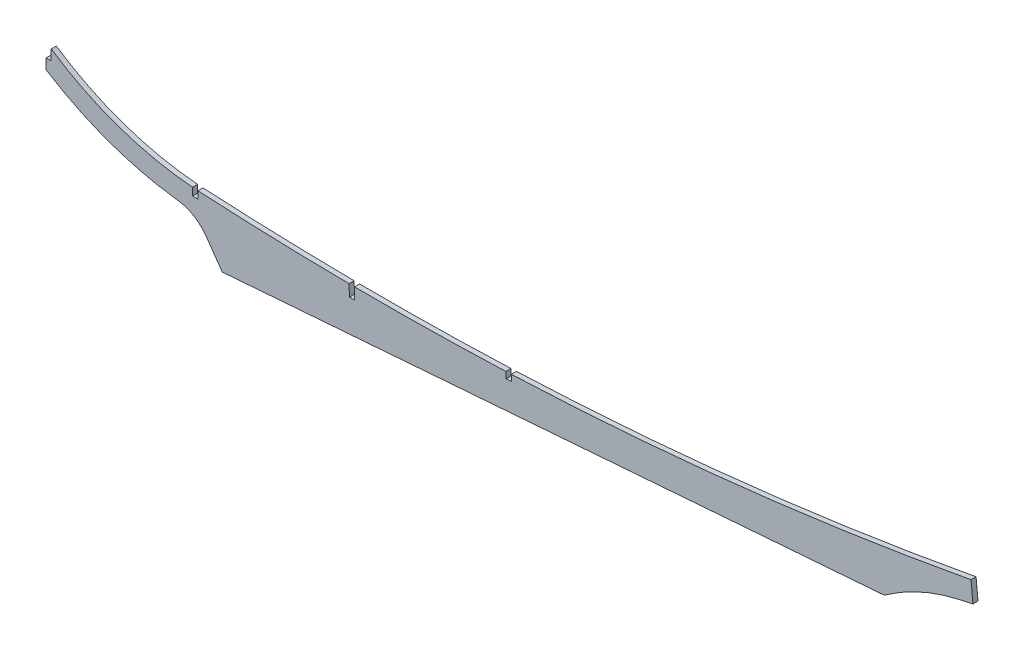
SolidWorks part; units mm, degrees
material "Plywood"
ref_plane "Front Plane" through (0, 0, 0) normal (0, 0, 1) x (1, 0, 0)
ref_plane "Top Plane" through (0, 0, 0) normal (0, 1, 0) x (1, 0, 0)
ref_plane "Right Plane" through (0, 0, 0) normal (1, 0, 0) x (0, 0, -1)
sketch "Sketch1" plane through (0, 0, 0) normal (0, 0, 1) x (1, 0, 0)
  line L0 (0, 0) -> (0, -82.26) construction
  line L1 (0, -194.8549) -> (0, 194.8549) construction
  line L2 (0, -97.5) -> (0, -91.4585)
  line L3 (93.98, 0) -> (93.98, -189.8775) construction
  line L4 (93.98, -128.27) -> (110.9865, -152.3377)
  line L5 (110.9865, -152.3377) -> (126.0572, -151.1732)
  line L6 (176.9893, -147.2378) -> (184.6207, -146.6482)
  line L7 (187.8005, -146.4025) -> (241.2203, -142.2748)
  line L8 (354.9586, -133.4865) -> (362.6867, -132.8893)
  line L9 (365.8665, -132.6436) -> (377.9741, -131.7081)
  line L10 (384.3024, -131.2191) -> (404.1694, -129.684)
  line L11 (408.5302, -129.3471) -> (419.9272, -128.4665)
  line L12 (441.1767, -126.8246) -> (527.7101, -120.1383)
  line L13 (441.1767, -126.8246) -> (527.7101, -120.1383)
  line L14 (110.9865, -152.3377) -> (527.7101, -120.1383)
  line L17 (527.7101, -120.1383) -> (550.2893, -104.3281)
  line L18 (583.5231, -97.0014) -> (582.2981, -84.3606)
  line L20 (110.9865, -152.3377) -> (126.0572, -151.1732)
  line L21 (550.2893, -104.3281) -> (583.5231, -97.0014)
  line L22 (0, 0) -> (690.5062, 0) construction
  line L23 (0, -91.4585) -> (3.81, -91.4585) construction
  line L24 (3.81, -91.4585) -> (3.81, -80.8129) construction
  line L25 (3.81, -84.8545) -> (0, -84.8545) construction
  line L26 (3.81, -91.4585) -> (3.81, -84.8545) construction
  line L27 (0, -84.8545) -> (0, -91.4585)
  line L28 (0, -91.4585) -> (0, -97.5) construction
  line L29 (0, -91.4585) -> (0, -84.8545) construction
  line L30 (0, -84.8545) -> (0, -82.26)
  line L31 (0, -82.26) -> (0, -84.8545) construction
  line L38 (278.6167, 141.3229) -> (279.2722, 126.0923)
  line L39 (189.035, 125.5168) -> (188.7159, 140.759) construction
  line L44 (185.8587, 125.447) -> (185.5396, 140.6895) construction
  line L57 (-1252.8442, 2935.2214) -> (-1204.869, 2833.9344) construction
  line L58 (281.7973, 141.4651) -> (282.4528, 126.2352)
  line L85 (185.8587, 125.447) -> (185.5396, 140.6895)
  line L88 (281.7973, 141.4651) -> (282.4528, 126.2352)
  line L89 (189.035, 125.5168) -> (188.7159, 140.759)
  line L91 (278.6167, 141.3229) -> (279.2722, 126.0923)
  arc A0 (0, -97.5) -> (93.98, -128.27) centre (107.2351, 71.12) ccw
  arc A1 (94.4926, -128.7218) -> (584.0826, -96.9366) centre (241.9639, 1386.2596) ccw construction
  arc A2 (3.81, -84.8545) -> (93.98, -115.5591) centre (107.2351, 71.12) ccw
  arc A3 (93.98, -115.5591) -> (582.2981, -84.3606) centre (209.0039, 1921.2601) ccw
  arc A4 (0, -82.26) -> (3.81, -84.8545) centre (107.2351, 71.12) ccw
  spline S0 degree 3 poles (188.7159, 140.759) (187.6572, 140.7359) (186.5984, 140.7127) (185.5396, 140.6895) knots 0 0 0 0 1 1 1 1 weights 1 1 1 1 construction
  spline S2 degree 3 poles (189.035, 125.5168) (187.9762, 125.4935) (186.9175, 125.4703) (185.8587, 125.447) knots 0 0 0 0 1 1 1 1 weights 1 1 1 1 construction
  spline S3 degree 3 poles (-1210.9259, -106.63) (-2775.9692, 118.2909) (2329.5489, 658.1971) (1983.6341, 70.2608) knots -1490.121028 -1490.121028 -1490.121028 -1490.121028 1121.542395 1121.542395 1121.542395 1121.542395 weights 3.048098 0.655832 0.359268 2.158404 only from (279.2722, 126.0923) to (282.4528, 126.2352)
  spline S5 degree 3 poles (2168.2812, 62.4493) (4677.1606, 1372.865) (-4077.6559, 154.0571) (-1330.4861, -129.027) knots -1401.84833 -1401.84833 -1401.84833 -1401.84833 1857.548452 1857.548452 1857.548452 1857.548452 weights 2.435358 0.211279 0.571848 3.517068 only from (281.7973, 141.4651) to (278.6167, 141.3229)
  spline S6 degree 3 poles (281.7973, 141.4651) (280.7371, 141.4178) (279.6769, 141.3704) (278.6167, 141.3229) knots 0 0 0 0 1 1 1 1 weights 1 1 1 1
  spline S7 degree 3 poles (279.2722, 126.0923) (280.3324, 126.14) (281.3926, 126.1876) (282.4528, 126.2352) knots 0 0 0 0 1 1 1 1 weights 1 1 1 1
  spline S9 degree 3 poles (3542.3692, 39.0953) (16953.6126, 2011.7323) (-10837.86, 256.2836) (-2684.9696, -115.914) knots -2918.044239 -2918.044239 -2918.044239 -2918.044239 3468.374997 3468.374997 3468.374997 3468.374997 weights 2.87602 0.139254 0.396818 3.648687 only from (189.035, 125.5168) to (185.8587, 125.447)
  spline S11 degree 3 poles (3867.0854, 32.7872) (100614.6923, 11738.557) (-16777.5539, 397.4867) (-2961.2542, -134.8273) knots -3513.558999 -3513.558999 -3513.558999 -3513.558999 4137.628718 4137.628718 4137.628718 4137.628718 weights 3.151493 0.02852 0.305376 3.982094 only from (188.7159, 140.759) to (185.5396, 140.6895)
  dimension "D3" = 71.12
  dimension "D5" = 35
  dimension "D6" = 3.81
  dimension "D8" = 97.0014
  dimension "D12" = 2040.0644
  dimension "D1" = 97.5
  dimension "D2" = 15.24
  dimension "D4" = 128.27
  dimension "D7" = 6.604
  dimension "D9" = 583.5231
  dimension "D10" = 12.7
  dimension "D11" = 96.898
  dimension "D13" = 120.1383
  dimension "D14" = 93.98
extrude "Boss-Extrude1" add sketch "Sketch1" along normal mid plane 3.175
fillet "Fillet1" radius 127 1 edges at (550.2893, -104.3281, 0)
fillet "Fillet2" radius 25.4 1 edges at (93.98, -128.27, 0)
sketch "Sketch2" plane through (0, 0, 1.5875) normal (0, 0, 1) x (1, 0, 0)
  line L0 (0, 0) -> (0, -91.1514) construction
  line L2 (0, 0) -> (93.98, 0) construction
  line L3 (0, -91.0752) -> (3.302, -91.0752)
  line L4 (0, -91.0752) -> (0, -78.3752)
  line L5 (0, -78.3752) -> (3.302, -78.3752)
  line L6 (3.302, -91.0752) -> (3.302, -78.3752)
  line L7 (93.98, 0) -> (711.1104, 0) construction
  line L9 (93.98, 0) -> (93.98, -120.3396) construction
  line L14 (192.6555, -126.071) -> (190.0163, 0) construction
  line L17 (92.2909, -120.2634) -> (95.6691, -120.2634)
  line L18 (92.2909, -120.2634) -> (92.2909, -107.5634)
  line L19 (95.6691, -120.2634) -> (95.6691, -107.5634)
  line L20 (92.2909, -107.5634) -> (95.6691, -107.5634)
  line L21 (190.9652, -126.0302) -> (194.3427, -125.9595)
  line L22 (190.9652, -126.0302) -> (190.6994, -113.333)
  line L23 (194.3427, -125.9595) -> (194.0769, -113.2623)
  line L24 (190.6994, -113.333) -> (194.0769, -113.2623)
  line L33 (289.698, -121.1534) -> (293.0731, -121.0082)
  line L34 (291.3888, -121.1569) -> (286.1742, 0) construction
  line L35 (289.698, -121.1534) -> (289.4249, -114.8093)
  line L36 (293.0731, -121.0082) -> (292.8, -114.664)
  line L37 (289.4249, -114.8093) -> (292.8, -114.664)
  point P10 (93.98, -107.5634)
  point P16 (192.3881, -113.2976)
  point P19 (291.3855, -121.0808)
  dimension "D1" = 91.1514
  dimension "D2" = 3.302
  dimension "D3" = 0.0762
  dimension "D4" = 93.98
  dimension "D5" = 91.199
  dimension "D6" = 96.0363
  dimension "D7" = 126.0986
  dimension "D8" = 120.3396
  dimension "D9" = 0.0762
  dimension "D10" = 3.3782
  dimension "D11" = 0.0762
  dimension "D12" = 3.3782
  dimension "D13" = 12.7
  dimension "D14" = 12.7
  dimension "D15" = 12.7
  dimension "D16" = 92.464
  dimension "D17" = 96.158
  dimension "D18" = 121.2691
  dimension "D19" = 0.0762
  dimension "D20" = 3.3782
  dimension "D21" = 6.35
extrude "Cut-Extrude1" cut sketch "Sketch2" against normal through all
